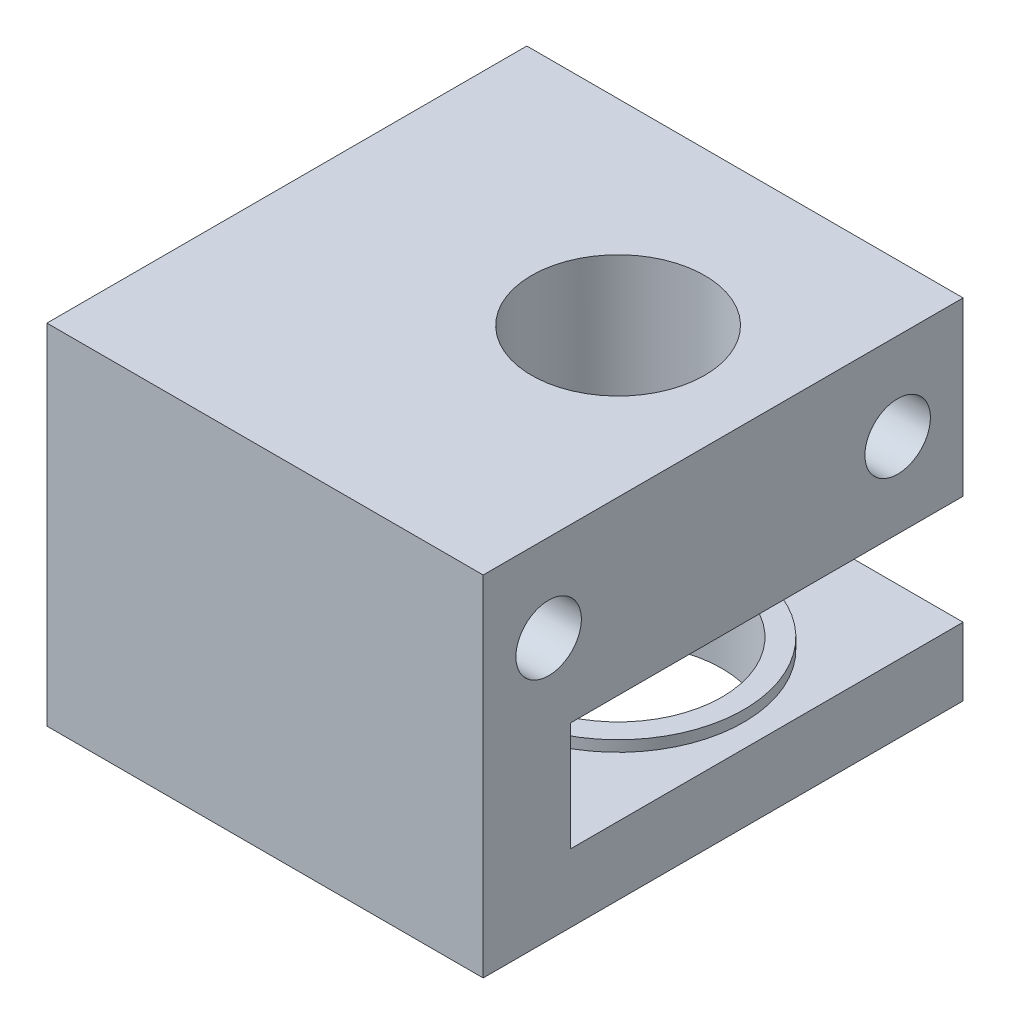
SolidWorks part; units mm, degrees
material "ABS"
ref_plane "Front Plane" through (0, 0, 0) normal (0, 0, 1) x (1, 0, 0)
ref_plane "Top Plane" through (0, 0, 0) normal (0, 1, 0) x (1, 0, 0)
ref_plane "Right Plane" through (0, 0, 0) normal (1, 0, 0) x (0, 0, -1)
sketch "Sketch1" plane through (0, 0, 0) normal (0, 1, 0) x (1, 0, 0)
  line L1 (0, 0) -> (20, 0)
  line L2 (0, 0) -> (0, 22)
  line L3 (0, 22) -> (20, 22)
  line L4 (20, 0) -> (20, 22)
  dimension "D1" = 22
  dimension "D2" = 20
extrude "Boss-Extrude1" add sketch "Sketch1" along normal blind 16
sketch "Sketch2" plane through (0, 0, -22) normal (0, 0, -1) x (-1, 0, 0)
  line L0 (-20, 8) -> (0, 8) construction
  line L1 (-20, 16) -> (-20, 0) construction
  line L2 (0, 16) -> (0, 0) construction
  line L3 (-20, 0) -> (0, 0) construction
  line L4 (-20, 3.125) -> (-5, 3.125)
  line L5 (-20, 3.125) -> (-20, 8.125)
  line L6 (-20, 8.125) -> (-5, 8.125)
  line L7 (-5, 3.125) -> (-5, 8.125)
  point P12 (0, 0)
  dimension "D1" = 15
  dimension "D2" = 5
  dimension "D3" = 3.125
extrude "Cut-Extrude1" cut sketch "Sketch2" against normal through all
sketch "Sketch3" plane through (0, 3.125, 0) normal (0, 1, 0) x (1, 0, 0)
  line L0 (20, 22) -> (5, 22) construction
  circle A0 centre (13.1845, 13) radius 3.9687
  point P5 (0, 0)
  dimension "D1" = 9
extrude "Cut-Extrude2" cut sketch "Sketch3" against normal through all both and the other way through all
sketch "Sketch4" plane through (0, 0, 0) normal (0, -1, 0) x (1, 0, 0)
  circle A0 centre (13.1845, -13) radius 4.7625
extrude "Cut-Extrude3" cut sketch "Sketch4" against normal up to next
sketch "Sketch5" plane through (0, 3.125, 0) normal (0, 1, 0) x (1, 0, 0)
  circle A0 centre (13.1845, 13) radius 4.7625
  circle A1 centre (13.1845, 13) radius 5.7625
  dimension "D1" = 1
extrude "Boss-Extrude2" add sketch "Sketch5" along normal blind 0.5
sketch "Sketch6" plane through (0, 8.125, 0) normal (0, -1, 0) x (1, 0, 0)
  circle A0 centre (13.1845, -13) radius 3.9687
  circle A1 centre (13.1845, -13) radius 5.2625
  dimension "D1" = 10.525
extrude "Boss-Extrude3" add sketch "Sketch6" along normal blind 0.5
sketch "Sketch7" plane through (0, 3.125, 0) normal (0, 1, 0) x (1, 0, 0)
  line L0 (20, 0) -> (20, 22) construction
  line L1 (5, 0) -> (20, 0)
  line L2 (5, 0) -> (5, 4)
  line L3 (5, 4) -> (20, 4)
  line L4 (20, 0) -> (20, 4)
  dimension "D1" = 4
extrude "Boss-Extrude4" add sketch "Sketch7" along normal through all
sketch "Sketch9" plane through (0, 0, 0) normal (-1, 0, 0) x (0, 0, 1)
  line L0 (-22, 16) -> (0, 16) construction
  line L1 (0, 16) -> (0, 0) construction
  line L2 (-22, 16) -> (-22, 0) construction
  line L3 (-22, 8) -> (0, 8) construction
  line L4 (-19, 8) -> (-19, 16) construction
  circle A0 centre (-3, 12) radius 1.5
  circle A1 centre (-19, 12) radius 1.5
  point P14 (0, 0)
  point P15 (-19, 12)
  point P16 (0, 0)
  dimension "D1" = 3
  dimension "D4" = 3
  dimension "D3" = 3
extrude "Cut-Extrude4" cut sketch "Sketch9" against normal through all
